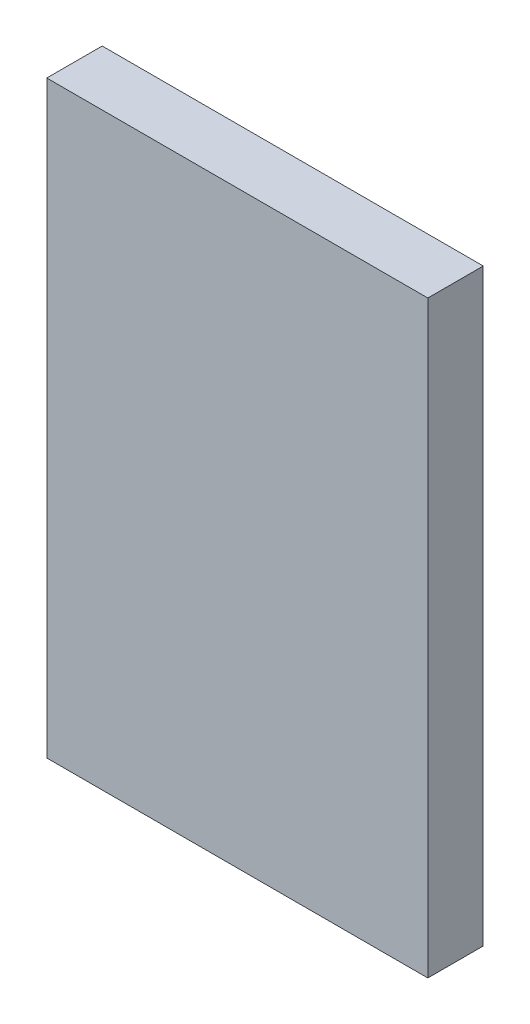
SolidWorks part; units mm, degrees
ref_plane "前视基准面" through (0, 0, 0) normal (0, 0, 1) x (1, 0, 0)
ref_plane "上视基准面" through (0, 0, 0) normal (0, 1, 0) x (1, 0, 0)
ref_plane "右视基准面" through (0, 0, 0) normal (1, 0, 0) x (0, 0, -1)
sketch "草图1" plane through (0, 0, 0) normal (0, 0, 1) x (1, 0, 0)
  line L0 (0, 6) -> (-5.5, 0)
  line L1 (11.5, -27) -> (-11.5, -27)
  line L2 (11.5, -27) -> (11.5, 27)
  line L3 (11.5, 27) -> (-11.5, 27)
  line L4 (-11.5, -27) -> (-11.5, 27)
  line L5 (0, 27) -> (0, -27) construction
  line L6 (11.5, 0) -> (-11.5, 0) construction
  line L7 (0, 6) -> (5.5, 0)
  line L8 (0, -6) -> (5.5, 0)
  line L9 (0, -6) -> (-5.5, 0)
  point P0 (0, 0)
  dimension "D1" = 23
  dimension "D2" = 54
  dimension "D3" = 6
  dimension "D4" = 6
extrude "凸台-拉伸1" add sketch "草图1" along normal blind 5
sketch "草图2" plane through (0, 0, 5) normal (0, 0, 1) x (1, 0, 0)
  line L0 (0, -6) -> (5.5, 0) construction
  line L1 (-5.5, 0) -> (0, -6) construction
  line L2 (0, 6) -> (-5.5, 0) construction
  line L3 (5.5, 0) -> (0, 6) construction
  line L4 (0, -6) -> (5.5, 0)
  line L5 (-5.5, 0) -> (0, -6)
  line L6 (0, 6) -> (-5.5, 0)
  line L7 (5.5, 0) -> (0, 6)
extrude "凸台-拉伸2" add sketch "草图2" against normal blind 3
sketch "草图3" plane through (0, 0, 5) normal (0, 0, 1) x (1, 0, 0)
  line L1 (27.5, -42.5) -> (-27.5, -42.5)
  line L2 (27.5, -42.5) -> (27.5, 42.5)
  line L3 (27.5, 42.5) -> (-27.5, 42.5)
  line L4 (-27.5, -42.5) -> (-27.5, 42.5)
  line L5 (0, 42.5) -> (0, -42.5) construction
  line L6 (27.5, 0) -> (-27.5, 0) construction
  point P0 (0, 0)
  dimension "D1" = 85
  dimension "D2" = 55
extrude "凸台-拉伸3" add sketch "草图3" along normal blind 8
